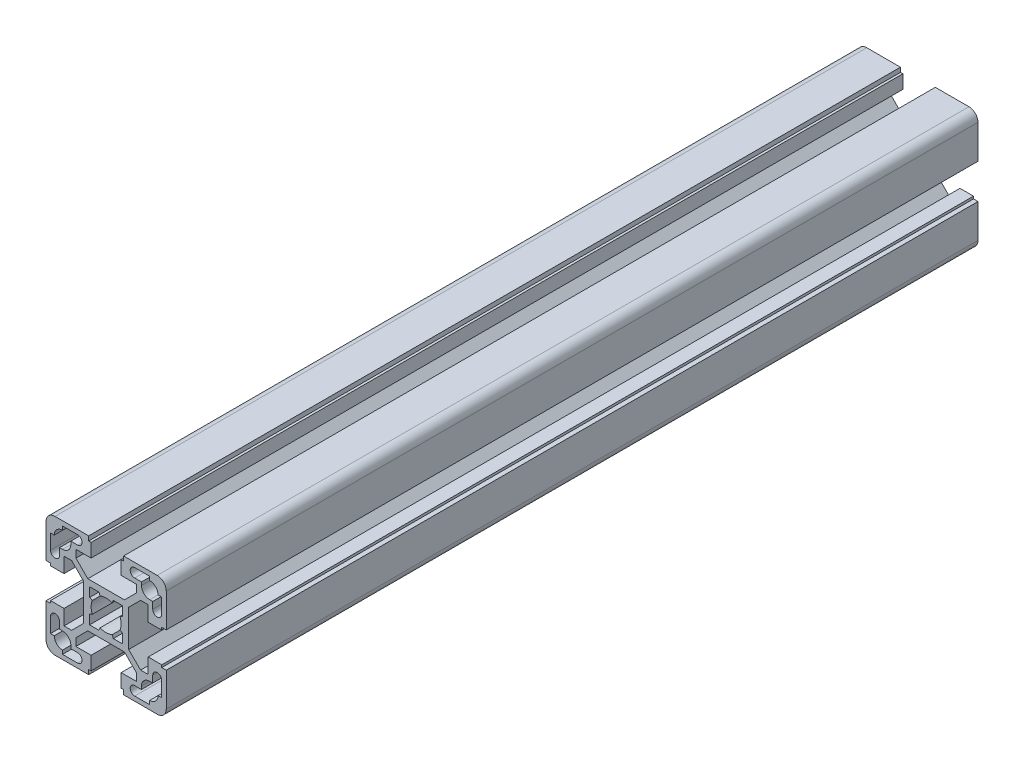
SolidWorks part; units mm, degrees
material "6061 Alloy"
ref_plane "Front Plane" through (0, 0, 0) normal (0, 0, 1) x (1, 0, 0)
ref_plane "Top Plane" through (0, 0, 0) normal (0, 1, 0) x (1, 0, 0)
ref_plane "Right Plane" through (0, 0, 0) normal (1, 0, 0) x (0, 0, -1)
sketch "Sketch1" plane through (0, 0, 0) normal (0, 0, 1) x (1, 0, 0)
  line L0 (5.8, -20) -> (17, -20)
  line L1 (14, -10.05) -> (11.4642, -10.05)
  line L2 (0, -21.1722) -> (0, 18.817) construction
  line L3 (0, 21.1722) -> (0, -18.817) construction
  line L4 (14.5, -18.5) -> (9.5, -18.5)
  line L5 (18.5, 5) -> (14, 5)
  line L6 (6.0858, -7.5) -> (10.05, -11.4642)
  line L7 (20, 5.8) -> (18.5, 5.8)
  line L8 (14, 5) -> (14, 10.05)
  line L9 (18.5, 5.8) -> (18.5, 5)
  line L10 (18.5, 14.5) -> (17.25, 14.5)
  line L11 (14.5, 11.75) -> (15.5, 11.75)
  line L12 (14.5, 17.25) -> (14.5, 18.5)
  line L13 (18.5, 9.5) -> (18.5, 14.5)
  line L14 (15.5, 11.75) -> (15.5, 9.5)
  line L15 (20, 17) -> (20, 5.8)
  line L16 (5.5, 5.5) -> (2.3979, 5.5)
  line L17 (2.3979, 5.5) -> (1.9983, 4.5833)
  line L18 (5.5, 2.3979) -> (5.5, 5.5)
  line L19 (4.5833, 1.9983) -> (5.5, 2.3979)
  line L20 (5, -14) -> (5, -18.5)
  line L21 (11.4642, 10.05) -> (7.5, 6.0858)
  line L22 (-6.0858, 7.5) -> (6.0858, 7.5)
  line L23 (11.75, 15.5) -> (11.75, 14.5)
  line L24 (5, -18.5) -> (5.8, -18.5)
  line L25 (5.8, -18.5) -> (5.8, -20)
  line L26 (10.05, -11.4642) -> (10.05, -14)
  line L27 (10.05, -14) -> (5, -14)
  line L28 (9.5, -15.5) -> (11.75, -15.5)
  line L29 (11.75, -15.5) -> (11.75, -14.5)
  line L30 (9.5, 15.5) -> (11.75, 15.5)
  line L31 (10.05, 14) -> (5, 14)
  line L32 (10.05, 11.4642) -> (10.05, 14)
  line L33 (5.8, 18.5) -> (5.8, 20)
  line L34 (5, 18.5) -> (5.8, 18.5)
  line L35 (7.5, -6.0858) -> (7.5, 6.0858)
  line L36 (5, 14) -> (5, 18.5)
  line L37 (6.0858, 7.5) -> (10.05, 11.4642)
  line L38 (14.5, 18.5) -> (9.5, 18.5)
  line L39 (14, 10.05) -> (11.4642, 10.05)
  line L40 (5.8, 20) -> (17, 20)
  line L41 (-18.5, -5) -> (-14, -5)
  line L42 (-6.0858, -7.5) -> (6.0858, -7.5)
  line L43 (11.4642, -10.05) -> (7.5, -6.0858)
  line L44 (-20, -5.8) -> (-18.5, -5.8)
  line L45 (-14, -5) -> (-14, -10.05)
  line L46 (-18.5, -5.8) -> (-18.5, -5)
  line L47 (-18.5, -14.5) -> (-17.25, -14.5)
  line L48 (4.5833, -1.9983) -> (5.5, -2.3979)
  line L49 (5.5, -2.3979) -> (5.5, -5.5)
  line L50 (2.3979, -5.5) -> (1.9983, -4.5833)
  line L51 (5.5, -5.5) -> (2.3979, -5.5)
  line L52 (-14.5, -11.75) -> (-15.5, -11.75)
  line L53 (-14.5, -17.25) -> (-14.5, -18.5)
  line L54 (-18.5, -9.5) -> (-18.5, -14.5)
  line L55 (-15.5, -11.75) -> (-15.5, -9.5)
  line L56 (-20, -17) -> (-20, -5.8)
  line L57 (-5.5, -5.5) -> (-2.3979, -5.5)
  line L58 (-2.3979, -5.5) -> (-1.9983, -4.5833)
  line L59 (-5.5, -2.3979) -> (-5.5, -5.5)
  line L60 (-4.5833, -1.9983) -> (-5.5, -2.3979)
  line L61 (-11.4642, -10.05) -> (-7.5, -6.0858)
  line L62 (-5.8, 20) -> (-17, 20)
  line L63 (-14, 10.05) -> (-11.4642, 10.05)
  line L64 (-14.5, 18.5) -> (-9.5, 18.5)
  line L65 (-6.0858, 7.5) -> (-10.05, 11.4642)
  line L66 (-5, 14) -> (-5, 18.5)
  line L67 (-7.5, -6.0858) -> (-7.5, 6.0858)
  line L68 (-5, 18.5) -> (-5.8, 18.5)
  line L69 (-5.8, 18.5) -> (-5.8, 20)
  line L70 (-10.05, 11.4642) -> (-10.05, 14)
  line L71 (-10.05, 14) -> (-5, 14)
  line L72 (-9.5, 15.5) -> (-11.75, 15.5)
  line L73 (-11.75, -15.5) -> (-11.75, -14.5)
  line L74 (-9.5, -15.5) -> (-11.75, -15.5)
  line L75 (-10.05, -14) -> (-5, -14)
  line L76 (-10.05, -11.4642) -> (-10.05, -14)
  line L77 (-5.8, -18.5) -> (-5.8, -20)
  line L78 (-5, -18.5) -> (-5.8, -18.5)
  line L79 (-11.75, 15.5) -> (-11.75, 14.5)
  line L80 (-11.4642, 10.05) -> (-7.5, 6.0858)
  line L81 (-5, -14) -> (-5, -18.5)
  line L82 (-4.5833, 1.9983) -> (-5.5, 2.3979)
  line L83 (-5.5, 2.3979) -> (-5.5, 5.5)
  line L84 (-2.3979, 5.5) -> (-1.9983, 4.5833)
  line L85 (-5.5, 5.5) -> (-2.3979, 5.5)
  line L86 (-20, 17) -> (-20, 5.8)
  line L87 (-15.5, 11.75) -> (-15.5, 9.5)
  line L88 (20, -17) -> (20, -5.8)
  line L89 (15.5, -11.75) -> (15.5, -9.5)
  line L90 (18.5, -9.5) -> (18.5, -14.5)
  line L91 (14.5, -17.25) -> (14.5, -18.5)
  line L92 (14.5, -11.75) -> (15.5, -11.75)
  line L93 (18.5, -14.5) -> (17.25, -14.5)
  line L94 (-18.5, 9.5) -> (-18.5, 14.5)
  line L95 (-14.5, 17.25) -> (-14.5, 18.5)
  line L96 (18.5, -5.8) -> (18.5, -5)
  line L97 (14, -5) -> (14, -10.05)
  line L98 (20, -5.8) -> (18.5, -5.8)
  line L99 (18.5, -5) -> (14, -5)
  line L100 (-14.5, 11.75) -> (-15.5, 11.75)
  line L101 (-18.5, 14.5) -> (-17.25, 14.5)
  line L102 (-18.5, 5.8) -> (-18.5, 5)
  line L103 (-14, 5) -> (-14, 10.05)
  line L104 (-20, 5.8) -> (-18.5, 5.8)
  line L105 (-6.0858, -7.5) -> (-10.05, -11.4642)
  line L106 (-18.5, 5) -> (-14, 5)
  line L107 (-14.5, -18.5) -> (-9.5, -18.5)
  line L108 (-20, 0) -> (20.788, 0) construction
  line L109 (-14, -10.05) -> (-11.4642, -10.05)
  line L110 (-5.8, -20) -> (-17, -20)
  arc A0 (14.5, -11.75) -> (11.75, -14.5) centre (14.5, -14.5) ccw
  arc A1 (18.5, 9.5) -> (15.5, 9.5) centre (17, 9.5) cw
  arc A2 (14.5, 17.25) -> (17.25, 14.5) centre (14.5, 14.5) cw
  arc A3 (17, 20) -> (20, 17) centre (17, 17) cw
  arc A4 (-1.9983, 4.5833) -> (1.9983, 4.5833) centre (0, 0) cw
  arc A5 (9.5, 15.5) -> (9.5, 18.5) centre (9.5, 17) cw
  arc A6 (9.5, -15.5) -> (9.5, -18.5) centre (9.5, -17) ccw
  arc A7 (14.5, 11.75) -> (11.75, 14.5) centre (14.5, 14.5) cw
  arc A8 (4.5833, -1.9983) -> (4.5833, 1.9983) centre (0, 0) ccw
  arc A9 (-18.5, -9.5) -> (-15.5, -9.5) centre (-17, -9.5) cw
  arc A10 (-14.5, -17.25) -> (-17.25, -14.5) centre (-14.5, -14.5) cw
  arc A11 (-1.9983, -4.5833) -> (1.9983, -4.5833) centre (0, 0) ccw
  arc A12 (-17, -20) -> (-20, -17) centre (-17, -17) cw
  arc A13 (-4.5833, -1.9983) -> (-4.5833, 1.9983) centre (0, 0) cw
  arc A14 (-14.5, 11.75) -> (-11.75, 14.5) centre (-14.5, 14.5) ccw
  arc A15 (-9.5, -15.5) -> (-9.5, -18.5) centre (-9.5, -17) cw
  arc A16 (-9.5, 15.5) -> (-9.5, 18.5) centre (-9.5, 17) ccw
  arc A17 (-17, 20) -> (-20, 17) centre (-17, 17) ccw
  arc A18 (17, -20) -> (20, -17) centre (17, -17) ccw
  arc A19 (14.5, -17.25) -> (17.25, -14.5) centre (14.5, -14.5) ccw
  arc A20 (18.5, -9.5) -> (15.5, -9.5) centre (17, -9.5) ccw
  arc A21 (-14.5, 17.25) -> (-17.25, 14.5) centre (-14.5, 14.5) ccw
  arc A22 (-18.5, 9.5) -> (-15.5, 9.5) centre (-17, 9.5) ccw
  arc A23 (-14.5, -11.75) -> (-11.75, -14.5) centre (-14.5, -14.5) cw
  point P55 (7.5, 0)
  point P101 (-7.5, 0)
  point P116 (0, -7.5)
  point P149 (0, 7.5)
extrude "Extrude1" add sketch "Sketch1" along normal blind 270
hole_wizard "M12 Tapped Hole1" [suppressed] positions "3DSketch2" profile "Sketch3" tap size "M12" standard "ISO"
sketch3d "3DSketch2"
  line L0 (-20, 17, 0) -> (-20, 5.8, 0) construction
  line L1 (-5.8, 20, 0) -> (-17, 20, 0) construction
  line L2 (-5.8, 20, 200) -> (-17, 20, 200) construction
  line L3 (-20, 17, 200) -> (-20, 5.8, 200) construction
  point P0 (0, 0, 200)
  point P2 (0, 0, 0)
  dimension "D1" = 20
  dimension "D2" = 20
  dimension "D3" = 20
  dimension "D4" = 20
sketch "Sketch3" plane through (0, 0, 200) normal (1, 0, 0) x (0, -1, 0)
  line L0 (0, 0) -> (0, 35.8144)
  line L1 (0, 35.8144) -> (5.1, 32.75)
  line L2 (5.1, 32.75) -> (5.1, 0.925)
  line L3 (5.1, 0.925) -> (6.025, 0)
  line L5 (6.025, 0) -> (0, 0)
  line L6 (-5.1, 0.925) -> (-6.025, 0) construction
  line L10 (0, 35.8144) -> (-5.1, 32.75) construction
  line L11 (0, -6.35) -> (0, 107.95) construction
  dimension "Tap Drill Dia." = 10.2
  dimension "Tap Drill Depth" = 32.75
  dimension "Near C'Sink Dia." = 12.05
  dimension "Near C'Sink Angle" = 90
  dimension "Drill Angle" = 118
cosmetic thread "Hole Thread1" [suppressed] parameters "D1"=24, "D2"=12
cosmetic thread "Hole Thread2" [suppressed] parameters "D1"=24, "D2"=12
hole_wizard "Ø9.8 (9.8) Diameter Hole1" [suppressed] positions "3DSketch3" profile "Sketch4" hole size "Ø9.8" standard "ISO"
sketch3d "3DSketch3"
  line L0 (-5.8, 20, 200) -> (-17, 20, 200) construction
  line L1 (20, -17, 200) -> (20, -5.8, 200) construction
  line L2 (17, 20, 0) -> (5.8, 20, 0) construction
  line L3 (20, -17, 0) -> (20, -5.8, 0) construction
  point P0 (0, 20, 184)
  point P2 (20, 0, 184)
  point P4 (0, 20, 16)
  point P6 (20, 0, 16)
  dimension "D1" = 16
  dimension "D2" = 20
  dimension "D3" = 20
  dimension "D4" = 16
  dimension "D5" = 16
  dimension "D6" = 16
sketch "Sketch4" plane through (0, 20, 184) normal (1, 0, 0) x (0, 0, 1)
  line L0 (0, 0) -> (0, 40)
  line L1 (0, 40) -> (4.9, 40)
  line L2 (4.9, 40) -> (4.9, 0)
  line L5 (4.9, 0) -> (0, 0)
  line L11 (0, -6.35) -> (0, 107.95) construction
  dimension "Thru Hole Dia." = 9.8
  dimension "Thru Hole Depth" = 40
hole_wizard "Ø17.0 (17) Diameter Hole1" [suppressed] positions "3DSketch4" profile "Sketch5" hole size "Ø17.0" standard "ISO"
sketch3d "3DSketch4"
  line L0 (-5.8, 20, 200) -> (-17, 20, 200) construction
  line L1 (-5.8, 20, 0) -> (-17, 20, 0) construction
  point P0 (0, 20, 177.5)
  point P2 (0, 20, 22.5)
  dimension "D1" = 20
  dimension "D2" = 22.5
  dimension "D3" = 22.5
sketch "Sketch5" plane through (0, 20, 177.5) normal (1, 0, 0) x (0, 0, 1)
  line L0 (0, 0) -> (0, 40)
  line L1 (0, 40) -> (8.5, 40)
  line L2 (8.5, 40) -> (8.5, 0)
  line L5 (8.5, 0) -> (0, 0)
  line L11 (0, -6.35) -> (0, 107.95) construction
  dimension "Thru Hole Dia." = 17
  dimension "Thru Hole Depth" = 40
